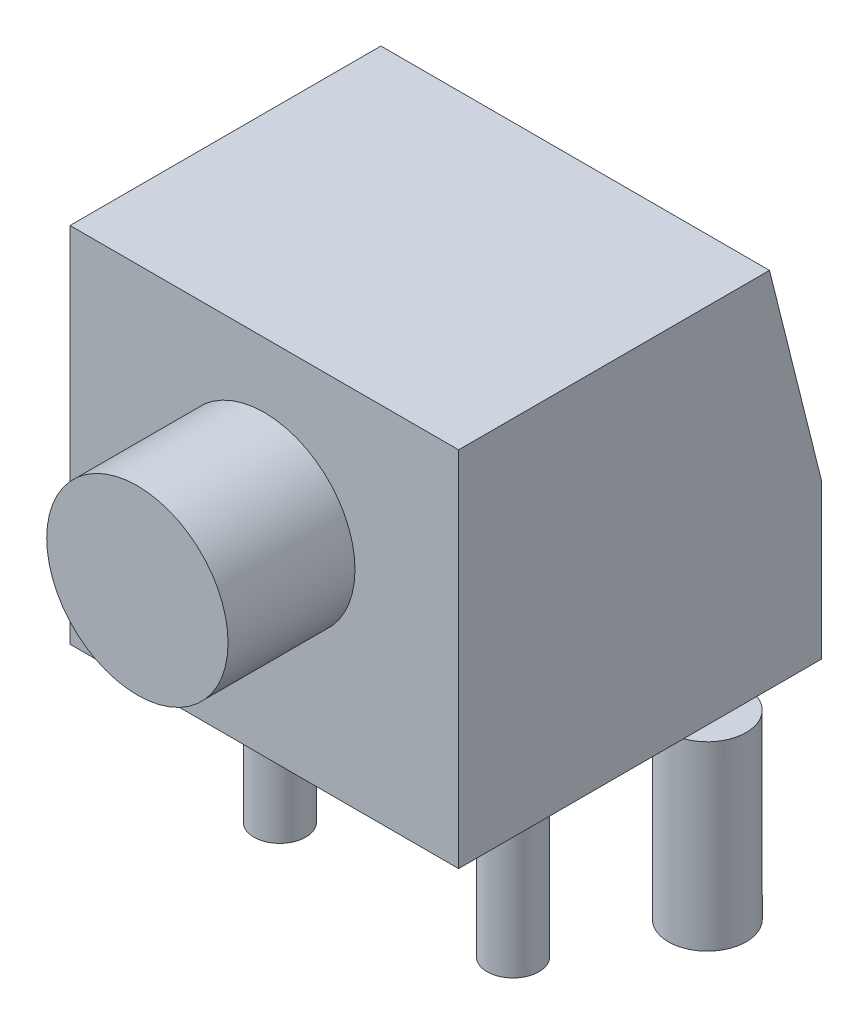
SolidWorks part; units mm, degrees
ref_plane "前视基准面" through (0, 0, 0) normal (0, 0, 1) x (1, 0, 0)
ref_plane "上视基准面" through (0, 0, 0) normal (0, 1, 0) x (1, 0, 0)
ref_plane "右视基准面" through (0, 0, 0) normal (1, 0, 0) x (0, 0, -1)
sketch "草图2" plane through (0, 0, 0) normal (1, 0, 0) x (0, 0, -1)
  line L1 (-2.55, 0) -> (4.45, 0)
  line L2 (-2.55, 0) -> (-2.55, 7)
  line L3 (-2.55, 7) -> (3.45, 7)
  line L4 (4.45, 0) -> (4.45, 3)
  line L7 (4.45, 3) -> (4.45, 7) construction
  line L8 (4.45, 7) -> (3.45, 7) construction
  line L9 (4.45, 3) -> (3.45, 7)
  dimension "D1" = 7
  dimension "D2" = 7
  dimension "D3" = 3
  dimension "D4" = 1
  dimension "D5" = 2.55
extrude "凸台-拉伸1" add sketch "草图2" along normal mid plane 7.5
sketch "草图4" plane through (0, 0, 0) normal (0, -1, 0) x (1, 0, 0)
  line L1 (3.85, 0) -> (-3.85, 0) construction
  line L3 (0, 0) -> (0, 50000) construction
  circle A0 centre (-3.5, -2.5) radius 0.75
  circle A1 centre (-2.25, 0) radius 0.5
  circle A2 centre (2.25, 0) radius 0.5
  circle A3 centre (3.5, -2.5) radius 0.75
  dimension "D1" = 1.5
  dimension "D2" = 1
  dimension "D3" = 2.5
  dimension "D4" = 4.5
  dimension "D5" = 7
extrude "凸台-拉伸3" add sketch "草图4" along normal blind 3.5
sketch "草图3" plane through (0, 0, 2.55) normal (0, 0, 1) x (1, 0, 0)
  circle A0 centre (0, 4) radius 1.75
  point P2 (0, 0)
  dimension "D2" = 3.5
  dimension "D1" = 4
extrude "凸台-拉伸2" add sketch "草图3" along normal offset from surface (2.45 mm away) 5 up to plane "前视基准面"
